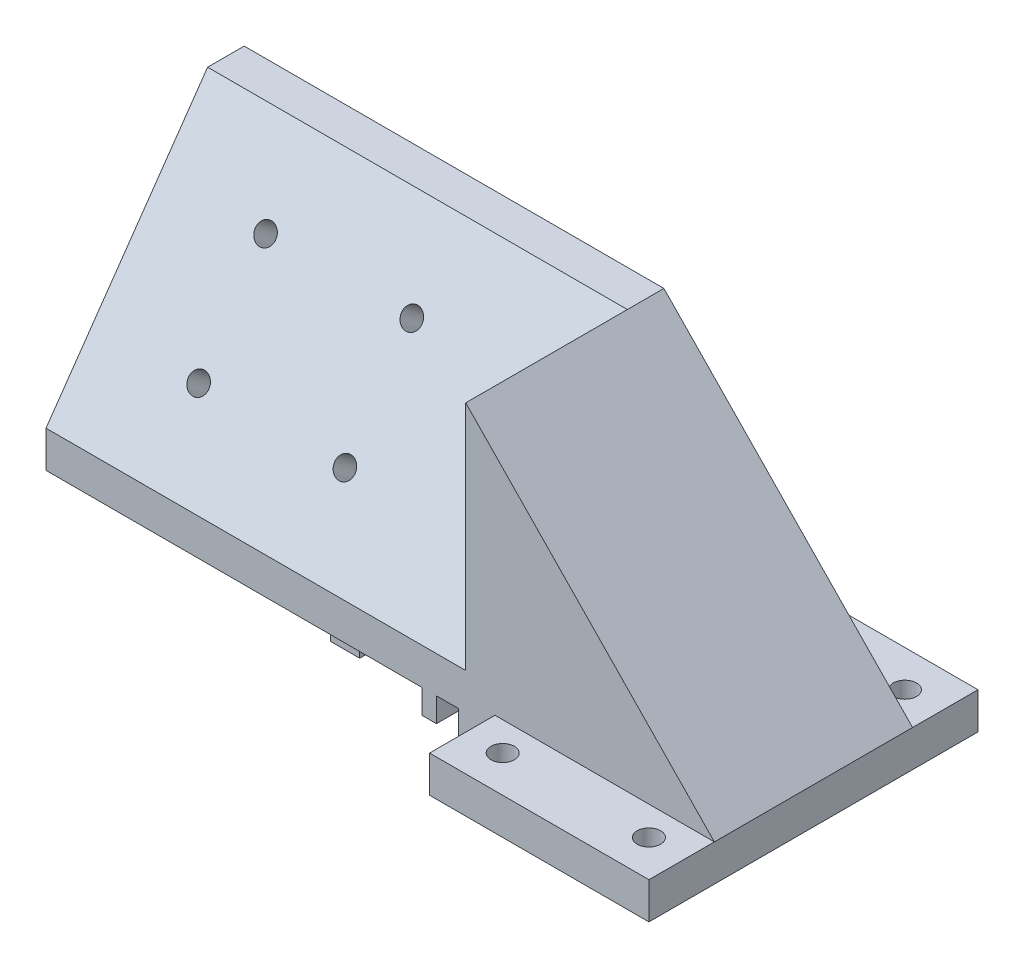
SolidWorks part; units mm, degrees
ref_plane "Front Plane" through (0, 0, 0) normal (0, 0, 1) x (1, 0, 0)
ref_plane "Top Plane" through (0, 0, 0) normal (0, 1, 0) x (1, 0, 0)
ref_plane "Right Plane" through (0, 0, 0) normal (1, 0, 0) x (0, 0, -1)
sketch "Sketch1" plane through (0, 0, 0) normal (0, 1, 0) x (1, 0, 0)
  line L1 (-15, 22.5) -> (15, 22.5)
  line L2 (-15, 22.5) -> (-15, -22.5)
  line L3 (-15, -22.5) -> (15, -22.5)
  line L4 (15, 22.5) -> (15, -22.5)
  line L5 (-15, 22.5) -> (15, -22.5) construction
  line L6 (-15, -22.5) -> (15, 22.5) construction
  line L7 (-6, 22.5) -> (6, 22.5)
  circle A0 centre (-10, 17.5) radius 1.6
  circle A1 centre (10, 17.5) radius 1.6
  circle A2 centre (10, -17.5) radius 1.6
  circle A3 centre (-10, -17.5) radius 1.6
  point P0 (0, 0)
  dimension "D3" = 5
  dimension "D4" = 5
  dimension "D5" = 3.2
  dimension "D8" = 5
  dimension "D9" = 5
  dimension "D10" = 5
  dimension "D1" = 30
  dimension "D2" = 45
  dimension "D6" = 2
  dimension "D7" = 2
extrude "Boss-Extrude3" add sketch "Sketch1" along normal blind 5
sketch "Sketch2" plane through (0, 5, 0) normal (0, 1, 0) x (1, 0, 0)
  line L0 (15, 22.5) -> (15, -22.5) construction
  line L1 (15, -13.55) -> (-15, -13.55)
  line L2 (15, -13.55) -> (15, 13.55)
  line L3 (15, 13.55) -> (-15, 13.55)
  line L4 (-15, -13.55) -> (-15, 13.55)
  line L5 (-15, 22.5) -> (-15, -22.5) construction
  line L7 (-15, 13.55) -> (-79, 13.55)
  line L8 (-15, 13.55) -> (-15, -13.55)
  line L9 (-15, -13.55) -> (-79, -13.55)
  line L10 (-79, 13.55) -> (-79, -13.55)
  circle A3 centre (10, 17.5) radius 1.6 construction
  circle A7 centre (10, -17.5) radius 1.6 construction
  line M8 (15, -22.5) -> (15, 22.5)
  line M14 (-15, 22.5) -> (-15, -22.5)
  dimension "D2" = 3.95
  dimension "D1" = 3.95
  dimension "D3" = 64
extrude "Boss-Extrude4" add sketch "Sketch2" along normal blind 35 and the other way blind 1.7 contours L7 L10 L9 M14 | L3 L1 M8 M14
sketch "Sketch3" plane through (0, 3.3, 0) normal (0, -1, 0) x (1, 0, 0)
  line L4 (-40, 11.05) -> (-40, -13.55)
  line L5 (-15, -13.55) -> (-79, -13.55) construction
  line L6 (-15, -22.5) -> (-15, 22.5) construction
  line L7 (-15, 13.55) -> (-79, 13.55) construction
  line L8 (-40, 11.05) -> (-36, 11.05)
  line L9 (-40, 11.05) -> (-40, -13.55)
  line L10 (-40, -13.55) -> (-36, -13.55)
  line L11 (-36, 11.05) -> (-36, -13.55)
  line L12 (-20, 13.55) -> (-15, 13.55)
  line L13 (-20, 13.55) -> (-20, -13.55)
  line L14 (-20, -13.55) -> (-15, -13.55)
  line L15 (-15, 13.55) -> (-15, -13.55)
  line L17 (-25, 13.55) -> (-23, 13.55)
  line L18 (-25, 13.55) -> (-25, -13.55)
  line L19 (-25, -13.55) -> (-23, -13.55)
  line L20 (-23, 13.55) -> (-23, -13.55)
  line M2 (-79, -13.55) -> (-15, -13.55)
  line M3 (-15, -13.55) -> (-15, 13.55)
  line M4 (-15, 13.55) -> (-79, 13.55)
  dimension "D1" = 25
  dimension "D2" = 4
  dimension "D3" = 5
  dimension "D4" = 2
  dimension "D5" = 3
extrude "Boss-Extrude5" add sketch "Sketch3" along normal blind 3.3 contours L11 L4 M4 M2 | L13 M4 M2 M3 | L20 L18 M4 M2
ref_plane "Plane1" through (0, 0, 0) normal (0, 0, -1) x (-1, 0, 0)
sketch "Sketch5" plane through (-79, 0, 0) normal (-1, 0, 0) x (0, 0, 1)
  line L8 (13.55, 3.3) -> (13.55, 8.3)
  line L9 (13.55, 3.3) -> (13.55, 40) construction
  line L13 (-13.55, 40) -> (-8.55, 40)
  line L14 (-13.55, 40) -> (13.55, 40) construction
  line L15 (13.55, 8.3) -> (-8.55, 40)
  line L16 (13.55, 8.3) -> (13.55, 40)
  line L17 (13.55, 40) -> (-8.55, 40)
  line M3 (13.55, 3.3) -> (13.55, 40)
  line M4 (13.55, 40) -> (-13.55, 40)
  dimension "D1" = 5
  dimension "D2" = 5
extrude "Cut-Extrude2" cut sketch "Sketch5" against normal blind 60 contours L15 M3 M4
sketch "Sketch6" plane through (0, 9.0715, 13.0121) normal (0, 0.5719, 0.8203) x (1, 0, 0)
  line L0 (-79, -0.9405) -> (-79, 37.7027) construction
  line L2 (-62, 26.3811) -> (-42, 26.3811) construction
  line L3 (-42, 26.3811) -> (-52, 26.3811) construction
  line L4 (-52, 37.7027) -> (-52, -0.9405) construction
  line L5 (-19, 37.7027) -> (-79, 37.7027) construction
  line L6 (-19, -0.9405) -> (-79, -0.9405) construction
  circle A0 centre (-62, 26.3811) radius 1.4
  circle A1 centre (-42, 26.3811) radius 1.4
  circle A2 centre (-42, 10.3811) radius 1.4
  circle A3 centre (-62, 10.3811) radius 1.4
  point P17 (-52, 18.3811)
  dimension "D1" = 2.8
  dimension "D2" = 17
  dimension "D3" = 2
  dimension "D5" = 20
  dimension "D6" = 16
  dimension "D7" = 16
  dimension "D8" = 8
  dimension "D4" = 2
extrude "Cut-Extrude3" cut sketch "Sketch6" against normal blind 39
sketch "Sketch7" plane through (-79, 0, 0) normal (-1, 0, 0) x (0, 0, 1)
  line L0 (13.55, 0) -> (13.55, 5) construction
  line L1 (-13.55, 40) -> (13.55, 40)
  line L2 (-13.55, 40) -> (-13.55, 3.3)
  line L3 (-13.55, 3.3) -> (13.55, 3.3)
  line L4 (13.55, 40) -> (13.55, 3.3)
  line L5 (13.55, 0) -> (13.55, 3.3) construction
extrude "Cut-Extrude4" cut sketch "Sketch7" against normal blind 2.6
ref_plane "Plane2" through (-52, 0, 0) normal (-1, 0, 0) x (0, 0, 1)
sketch "Sketch10" plane through (-52, 0, 0) normal (-1, 0, 0) x (0, 0, 1)
  line L11 (-13.55, 35) -> (-13.55, 3.3)
  line L12 (-13.55, 3.3) -> (8.55, 3.3)
  line L14 (-11.1593, 35) -> (-13.55, 35)
  line L15 (8.55, 3.3) -> (8.55, 6.7291)
  line L16 (8.55, 6.7291) -> (-11.1593, 35)
  line L17 (-11.1593, 35) -> (-13.55, 35)
  line L18 (8.55, 3.3) -> (8.55, 6.7291)
  line L41 (8.55, 6.7291) -> (-11.1593, 35)
  dimension "D1" = 5
extrude "Cut-Extrude5" cut sketch "Sketch10" against normal blind 15 and the other way blind 15
sketch "Sketch11" plane through (-76.4, 0, 0) normal (-1, 0, 0) x (0, 0, 1)
  line L10 (-13.55, 35) -> (-13.55, 3.3)
  line L11 (-13.55, 3.3) -> (8.55, 3.3)
  line L12 (8.55, 3.3) -> (8.55, 6.7291)
  line L13 (8.55, 6.7291) -> (-11.1593, 35)
  line L14 (-11.1593, 35) -> (-13.55, 35)
extrude "Cut-Extrude6" cut sketch "Sketch11" against normal blind 9.4
sketch "Sketch12" plane through (0, 0, 13.55) normal (0, 0, 1) x (1, 0, 0)
  line L0 (-19, 40) -> (15, 5)
  line L1 (15, 5) -> (15, 40)
  line L2 (15, 40) -> (-19, 40)
extrude "Cut-Extrude7" cut sketch "Sketch12" against normal through all
fillet "Fillet1" radius 2 1 edges at (-37, 20.8646, -1.3047)
